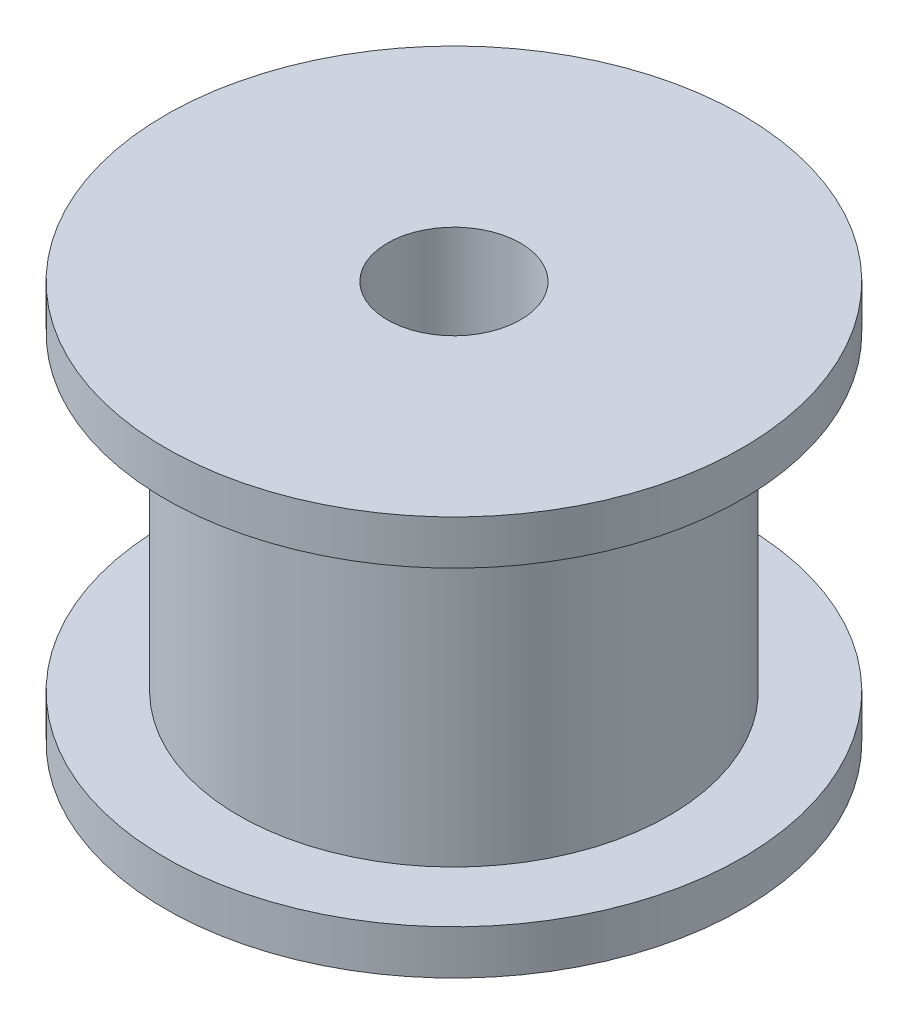
SolidWorks part; units mm, degrees
ref_plane "Спереди" through (0, 0, 0) normal (0, 0, 1) x (1, 0, 0)
ref_plane "Сверху" through (0, 0, 0) normal (0, 1, 0) x (1, 0, 0)
ref_plane "Справа" through (0, 0, 0) normal (1, 0, 0) x (0, 0, -1)
sketch "Sketch2" plane through (0, 0, 0) normal (1, 0, 0) x (0, 0, -1)
  line L0 (4.85, 3.9838) -> (4.85, -3.0162)
  line L1 (4.85, -3.0162) -> (6.5, -3.0162)
  line L2 (6.5, -3.0162) -> (6.5, -4.0162)
  line L3 (6.5, -4.0162) -> (1.5, -4.0162)
  line L4 (1.5, -4.0162) -> (1.5, 4.9838)
  line L5 (1.5, 4.9838) -> (6.5, 4.9838)
  line L6 (6.5, 4.9838) -> (6.5, 3.9838)
  line L7 (6.5, 3.9838) -> (4.85, 3.9838)
  line L8 (0, 0) -> (0, 3.7411) construction
  dimension "D1" = 1
  dimension "D2" = 1
  dimension "D3" = 9
  dimension "D4" = 9.7
  dimension "D5" = 13
  dimension "D6" = 3
revolve "Revolve1" add sketch "Sketch2" angle 360 about L8
